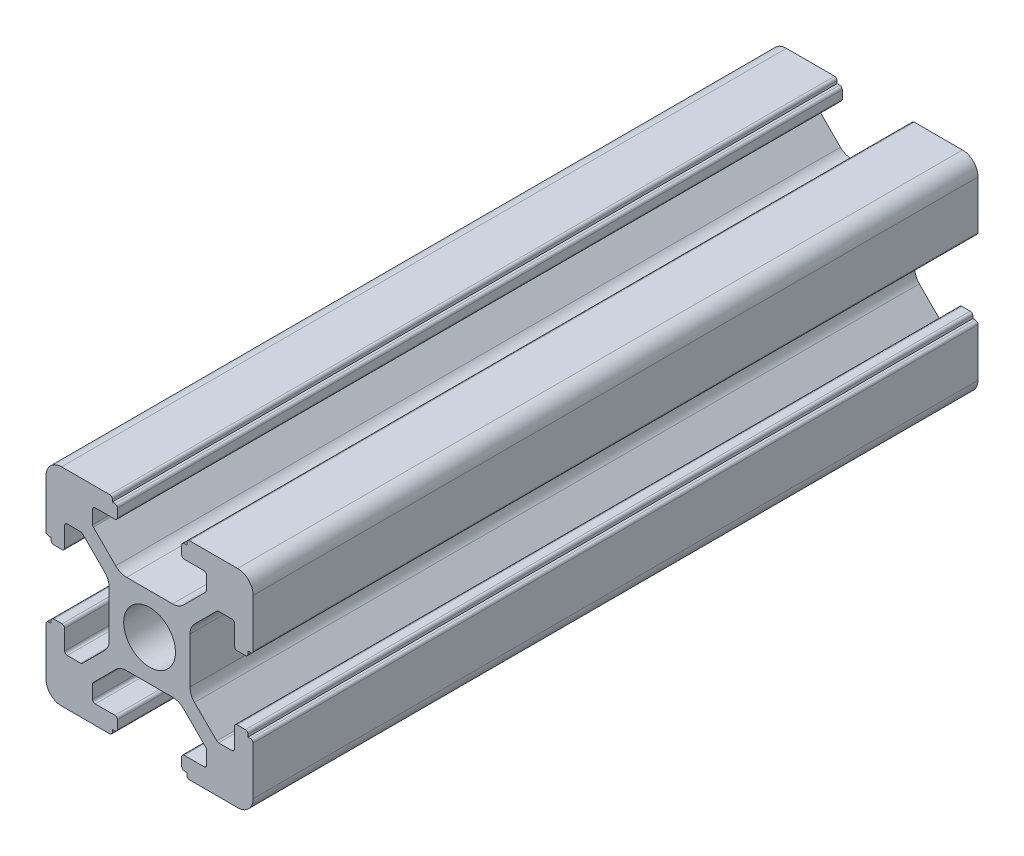
SolidWorks part; units mm, degrees
ref_plane "前视基准面" through (0, 0, 0) normal (0, 0, 1) x (1, 0, 0)
ref_plane "上视基准面" through (0, 0, 0) normal (0, 1, 0) x (1, 0, 0)
ref_plane "右视基准面" through (0, 0, 0) normal (1, 0, 0) x (0, 0, -1)
sketch "草图1" plane through (0, 0, 0) normal (0, 0, 1) x (1, 0, 0)
  line L0 (0, 0) -> (0, 5.5) construction
  line L1 (-8.5023, -10.0023) -> (-3.85, -10.0023)
  line L2 (-10.0023, -8.5023) -> (-10.0023, -3.85)
  line L3 (-8.5023, 10.0023) -> (-3.85, 10.0023)
  line L4 (10.0023, -8.5023) -> (10.0023, -3.85)
  line L5 (-10.0023, -10.0023) -> (10.0023, 10.0023) construction
  line L6 (-10.0023, 10.0023) -> (10.0023, -10.0023) construction
  line L7 (-2.218, -3.9) -> (2.218, -3.9)
  line L8 (-3.9, -2.218) -> (-3.9, 2.218)
  line L9 (-2.218, 3.9) -> (2.218, 3.9)
  line L10 (3.9, -2.218) -> (3.9, 2.218)
  line L11 (-3.9, -3.9) -> (3.9, 3.9) construction
  line L12 (-3.9, 3.9) -> (3.9, -3.9) construction
  line L13 (-5.25, -8.2) -> (-3.35, -8.2)
  line L14 (-8.2, -5.25) -> (-8.2, -3.35)
  line L15 (-5.25, 8.2) -> (-3.35, 8.2)
  line L16 (8.2, -5.25) -> (8.2, -3.35)
  line L17 (-8.2, -8.2) -> (8.2, 8.2) construction
  line L18 (-8.2, 8.2) -> (8.2, -8.2) construction
  line L19 (-7.95, 5.5) -> (-6.6642, 5.5)
  line L20 (0, 0) -> (5.5, 0) construction
  line L23 (-5.5, 7.95) -> (-5.5, 6.6642)
  line L26 (0, 0) -> (-0.5303, 0.5303)
  line L27 (3.2787, 4.3393) -> (5.4268, 6.4874)
  line L28 (0, 0) -> (0.5303, -0.5303)
  line L29 (5.5, 6.6642) -> (5.5, 7.95)
  line L30 (4.3393, 3.2787) -> (6.4874, 5.4268)
  line L31 (6.6642, 5.5) -> (7.95, 5.5)
  line L32 (4.3393, -3.2787) -> (6.4874, -5.4268)
  line L33 (3.2787, -4.3393) -> (5.4268, -6.4874)
  line L34 (-3.2787, -4.3393) -> (-5.4268, -6.4874)
  line L35 (-4.3393, -3.2787) -> (-6.4874, -5.4268)
  line L36 (-4.3393, 3.2787) -> (-6.4874, 5.4268)
  line L37 (-3.2787, 4.3393) -> (-5.4268, 6.4874)
  line L38 (3.1, -8.45) -> (3.1, -9.2523)
  line L39 (8.45, 3.1) -> (9.2523, 3.1)
  line L40 (-5.5, -6.6642) -> (-5.5, -7.95)
  line L41 (-6.6642, -5.5) -> (-7.95, -5.5)
  line L42 (5.5, -6.6642) -> (5.5, -7.95)
  line L43 (6.6642, -5.5) -> (7.95, -5.5)
  line L44 (9.2523, -3.1) -> (8.45, -3.1)
  line L46 (10.0023, 3.85) -> (10.0023, 8.5023)
  line L47 (8.2, 3.35) -> (8.2, 5.25)
  line L48 (-3.1, -9.2523) -> (-3.1, -8.45)
  line L49 (-8.45, -3.1) -> (-9.2523, -3.1)
  line L50 (-9.2523, 3.1) -> (-8.45, 3.1)
  line L51 (-3.1, 8.45) -> (-3.1, 9.2523)
  line L52 (3.1, 9.2523) -> (3.1, 8.45)
  line L53 (3.85, 10.0023) -> (8.5023, 10.0023)
  line L54 (3.35, 8.2) -> (5.25, 8.2)
  line L55 (-10.0023, 3.85) -> (-10.0023, 8.5023)
  line L56 (-8.2, 3.35) -> (-8.2, 5.25)
  line L57 (3.35, -8.2) -> (5.25, -8.2)
  line L58 (3.85, -10.0023) -> (8.5023, -10.0023)
  line L59 (9.7523, -3.6) -> (9.5023, -3.6)
  line L61 (9.7523, 3.6) -> (9.5023, 3.6)
  line L62 (9.5023, -3.6) -> (9.5023, -3.35)
  line L63 (3.6, -9.7523) -> (3.6, -9.5023)
  line L64 (3.35, -9.5023) -> (3.6, -9.5023)
  line L65 (9.5023, 3.35) -> (9.5023, 3.6)
  line L66 (-3.6, -9.5023) -> (-3.35, -9.5023)
  line L67 (-3.6, -9.7523) -> (-3.6, -9.5023)
  line L68 (-9.7523, -3.6) -> (-9.5023, -3.6)
  line L69 (-9.5023, -3.35) -> (-9.5023, -3.6)
  line L70 (-9.5023, 3.6) -> (-9.5023, 3.35)
  line L71 (-9.7523, 3.6) -> (-9.5023, 3.6)
  line L72 (-3.6, 9.7523) -> (-3.6, 9.5023)
  line L73 (-3.35, 9.5023) -> (-3.6, 9.5023)
  line L74 (3.6, 9.5023) -> (3.35, 9.5023)
  line L75 (3.6, 9.7523) -> (3.6, 9.5023)
  circle A0 centre (0, 0) radius 2.5
  arc A1 (10.0023, 8.5023) -> (8.5023, 10.0023) centre (8.5023, 8.5023) ccw
  arc A2 (8.5023, -10.0023) -> (10.0023, -8.5023) centre (8.5023, -8.5023) ccw
  arc A3 (-10.0023, -8.5023) -> (-8.5023, -10.0023) centre (-8.5023, -8.5023) ccw
  arc A4 (-10.0023, 8.5023) -> (-8.5023, 10.0023) centre (-8.5023, 8.5023) cw
  arc A5 (-9.5023, -3.35) -> (-9.2523, -3.1) centre (-9.2523, -3.35) cw
  arc A6 (-9.7523, -3.6) -> (-10.0023, -3.85) centre (-9.7523, -3.85) ccw
  arc A7 (-8.45, -3.1) -> (-8.2, -3.35) centre (-8.45, -3.35) cw
  arc A8 (-7.95, -5.5) -> (-8.2, -5.25) centre (-7.95, -5.25) cw
  arc A9 (-6.4874, -5.4268) -> (-6.6642, -5.5) centre (-6.6642, -5.25) cw
  arc A10 (-5.4268, -6.4874) -> (-5.5, -6.6642) centre (-5.25, -6.6642) ccw
  arc A11 (-5.5, -7.95) -> (-5.25, -8.2) centre (-5.25, -7.95) ccw
  arc A12 (-3.6, -9.7523) -> (-3.85, -10.0023) centre (-3.85, -9.7523) cw
  arc A13 (-3.35, -9.5023) -> (-3.1, -9.2523) centre (-3.35, -9.2523) ccw
  arc A14 (-3.1, -8.45) -> (-3.35, -8.2) centre (-3.35, -8.45) ccw
  arc A15 (3.1, -8.45) -> (3.35, -8.2) centre (3.35, -8.45) cw
  arc A16 (5.5, -7.95) -> (5.25, -8.2) centre (5.25, -7.95) cw
  arc A17 (5.4268, -6.4874) -> (5.5, -6.6642) centre (5.25, -6.6642) cw
  arc A18 (6.4874, -5.4268) -> (6.6642, -5.5) centre (6.6642, -5.25) ccw
  arc A19 (7.95, -5.5) -> (8.2, -5.25) centre (7.95, -5.25) ccw
  arc A20 (8.45, -3.1) -> (8.2, -3.35) centre (8.45, -3.35) ccw
  arc A21 (9.5023, -3.35) -> (9.2523, -3.1) centre (9.2523, -3.35) ccw
  arc A22 (9.7523, -3.6) -> (10.0023, -3.85) centre (9.7523, -3.85) cw
  arc A23 (3.35, -9.5023) -> (3.1, -9.2523) centre (3.35, -9.2523) cw
  arc A24 (3.6, -9.7523) -> (3.85, -10.0023) centre (3.85, -9.7523) ccw
  arc A25 (7.95, 5.5) -> (8.2, 5.25) centre (7.95, 5.25) cw
  arc A26 (8.2, 3.35) -> (8.45, 3.1) centre (8.45, 3.35) ccw
  arc A27 (9.5023, 3.35) -> (9.2523, 3.1) centre (9.2523, 3.35) cw
  arc A28 (9.7523, 3.6) -> (10.0023, 3.85) centre (9.7523, 3.85) ccw
  arc A29 (6.6642, 5.5) -> (6.4874, 5.4268) centre (6.6642, 5.25) ccw
  arc A30 (5.4268, 6.4874) -> (5.5, 6.6642) centre (5.25, 6.6642) ccw
  arc A31 (5.5, 7.95) -> (5.25, 8.2) centre (5.25, 7.95) ccw
  arc A32 (3.1, 8.45) -> (3.35, 8.2) centre (3.35, 8.45) ccw
  arc A33 (3.6, 9.7523) -> (3.85, 10.0023) centre (3.85, 9.7523) cw
  arc A34 (3.35, 9.5023) -> (3.1, 9.2523) centre (3.35, 9.2523) ccw
  arc A35 (-9.7523, 3.6) -> (-10.0023, 3.85) centre (-9.7523, 3.85) cw
  arc A36 (-9.5023, 3.35) -> (-9.2523, 3.1) centre (-9.2523, 3.35) ccw
  arc A37 (-8.45, 3.1) -> (-8.2, 3.35) centre (-8.45, 3.35) ccw
  arc A38 (-8.2, 5.25) -> (-7.95, 5.5) centre (-7.95, 5.25) cw
  arc A39 (-6.4874, 5.4268) -> (-6.6642, 5.5) centre (-6.6642, 5.25) ccw
  arc A40 (-5.4268, 6.4874) -> (-5.5, 6.6642) centre (-5.25, 6.6642) cw
  arc A41 (-5.5, 7.95) -> (-5.25, 8.2) centre (-5.25, 7.95) cw
  arc A42 (-3.1, 8.45) -> (-3.35, 8.2) centre (-3.35, 8.45) cw
  arc A43 (-3.1, 9.2523) -> (-3.35, 9.5023) centre (-3.35, 9.2523) ccw
  arc A44 (-3.6, 9.7523) -> (-3.85, 10.0023) centre (-3.85, 9.7523) ccw
  arc A45 (-4.3393, 3.2787) -> (-3.9, 2.218) centre (-5.4, 2.218) cw
  arc A46 (-3.2787, 4.3393) -> (-2.218, 3.9) centre (-2.218, 5.4) ccw
  arc A47 (3.2787, 4.3393) -> (2.218, 3.9) centre (2.218, 5.4) cw
  arc A48 (4.3393, 3.2787) -> (3.9, 2.218) centre (5.4, 2.218) ccw
  arc A49 (4.3393, -3.2787) -> (3.9, -2.218) centre (5.4, -2.218) cw
  arc A50 (3.2787, -4.3393) -> (2.218, -3.9) centre (2.218, -5.4) ccw
  arc A51 (-4.3393, -3.2787) -> (-3.9, -2.218) centre (-5.4, -2.218) ccw
  arc A52 (-2.218, -3.9) -> (-3.2787, -4.3393) centre (-2.218, -5.4) ccw
  point P0 (0, 0)
  point P7 (10.0023, 0)
  point P62 (0, 0)
  point P76 (0, 0)
  point P92 (-8.2, -5.5)
  point P99 (0, 0)
  point P106 (-5.5, -8.2)
  point P117 (5.5, -8.2)
  point P124 (8.2, -5.5)
  point P137 (8.2, 5.5)
  point P140 (8.2, 3.1)
  point P147 (6.5607, 5.5)
  point P152 (5.5, 8.2)
  point P167 (-8.2, 5.5)
  point P174 (-5.5, 8.2)
  dimension "D1" = 1.5
  dimension "D5" = 0.25
  dimension "D6" = 1.5
  dimension "D2" = 4
  dimension "D3" = 4
  dimension "D4" = 4
extrude "凸台-拉伸1" add sketch "草图1" along normal blind 70 contours A52 L7 A50 L33 A17 L42 A16 L57 A15 L38 A23 L64 L63 A24 L58 A2 L4 A22 L59 L62 A21 L44 A20 L16 A19 L43 A18 L32 A49 L10 A48 L30 A29 L31 A25 L47 A26 L39 A27 L65 L61 A28 L46 A1 L53 A33 L75 L74 A34 L52 A32
